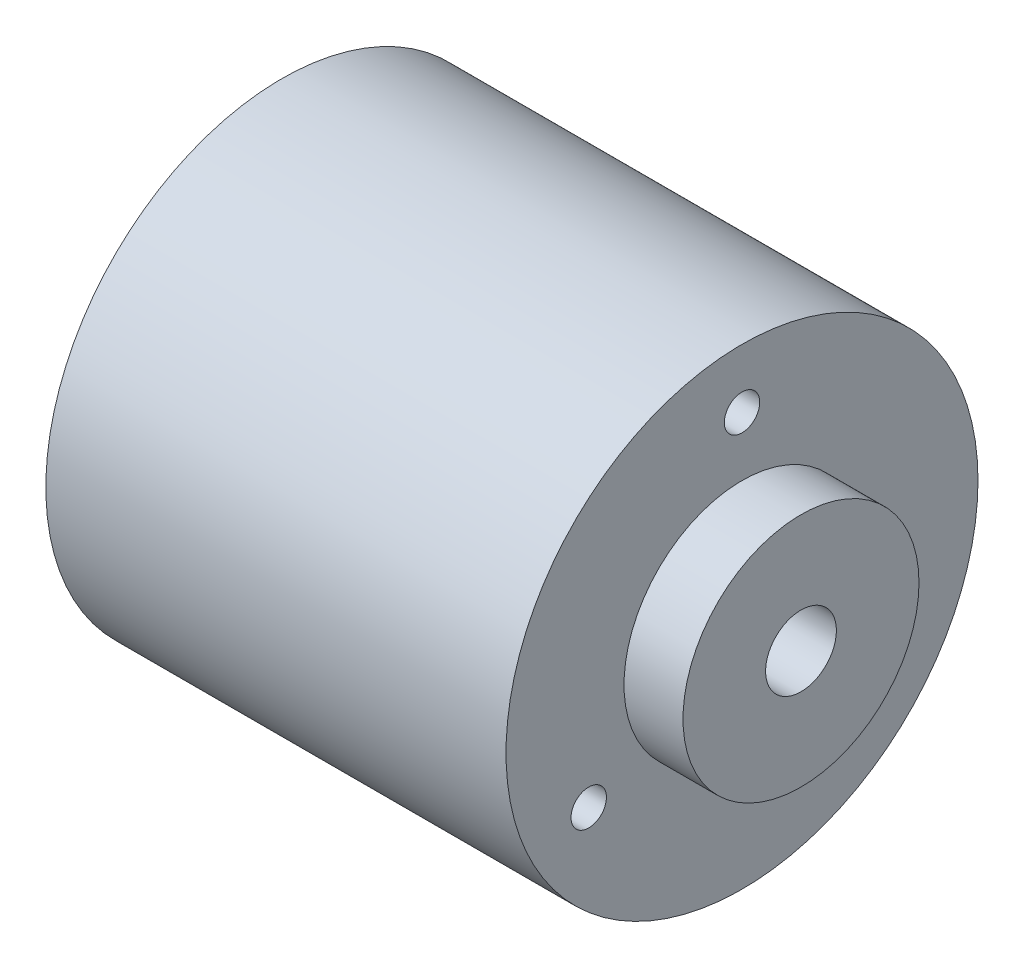
SolidWorks part; units mm, degrees
ref_plane "Ön Düzlem" through (0, 0, 0) normal (0, 0, 1) x (1, 0, 0)
ref_plane "Üst Düzlem" through (0, 0, 0) normal (0, 1, 0) x (1, 0, 0)
ref_plane "Sağ Düzlem" through (0, 0, 0) normal (1, 0, 0) x (0, 0, -1)
sketch "Sketch1" plane through (0, 0, 0) normal (1, 0, 0) x (0, 0, -1)
  circle A0 centre (0, 0) radius 20
extrude "Boss-Extrude1" add sketch "Sketch1" along normal blind 39
sketch "Sketch2" plane through (39, 0, 0) normal (1, 0, 0) x (0, 0, -1)
  circle A0 centre (0, 0) radius 10
extrude "Boss-Extrude2" add sketch "Sketch2" along normal blind 5
sketch "Sketch3" plane through (44, 0, 0) normal (1, 0, 0) x (0, 0, -1)
  circle A0 centre (0, 0) radius 3
sketch "Sketch5" plane through (39, 0, 0) normal (1, 0, 0) x (0, 0, -1)
  point P0 (0, 15)
  point P4 (12.9904, -7.5)
  point P5 (-12.9904, -7.5)
  point P6 (0, 0)
  dimension "D2" = 15
  dimension "D1" = 3
hole_wizard "Ø3.0mm Dowel Hole1" positions "3DSketch1" profile "Sketch6" hole size "Ø3.0" standard "ANSI Metric"
sketch3d "3DSketch1"
  point P0 (39, 15, 0)
  point P3 (39, -7.5, -12.9904)
  point P6 (39, -7.5, 12.9904)
sketch "Sketch6" plane through (39, 15, 0) normal (0, 1, 0) x (0, 0, -1)
  line L0 (0, 0) -> (0, 7.9013)
  line L1 (0, 7.9013) -> (1.5, 7)
  line L2 (1.5, 7) -> (1.5, 0)
  line L5 (1.5, 0) -> (0, 0)
  line L10 (0, 7.9013) -> (-1.5, 7) construction
  line L11 (0, -6.35) -> (0, 107.95) construction
  dimension "Hole Dia." = 3
  dimension "Hole Depth" = 7
  dimension "Drill Angle" = 118
extrude "Cut-Extrude2" cut sketch "Sketch3" against normal blind 5
